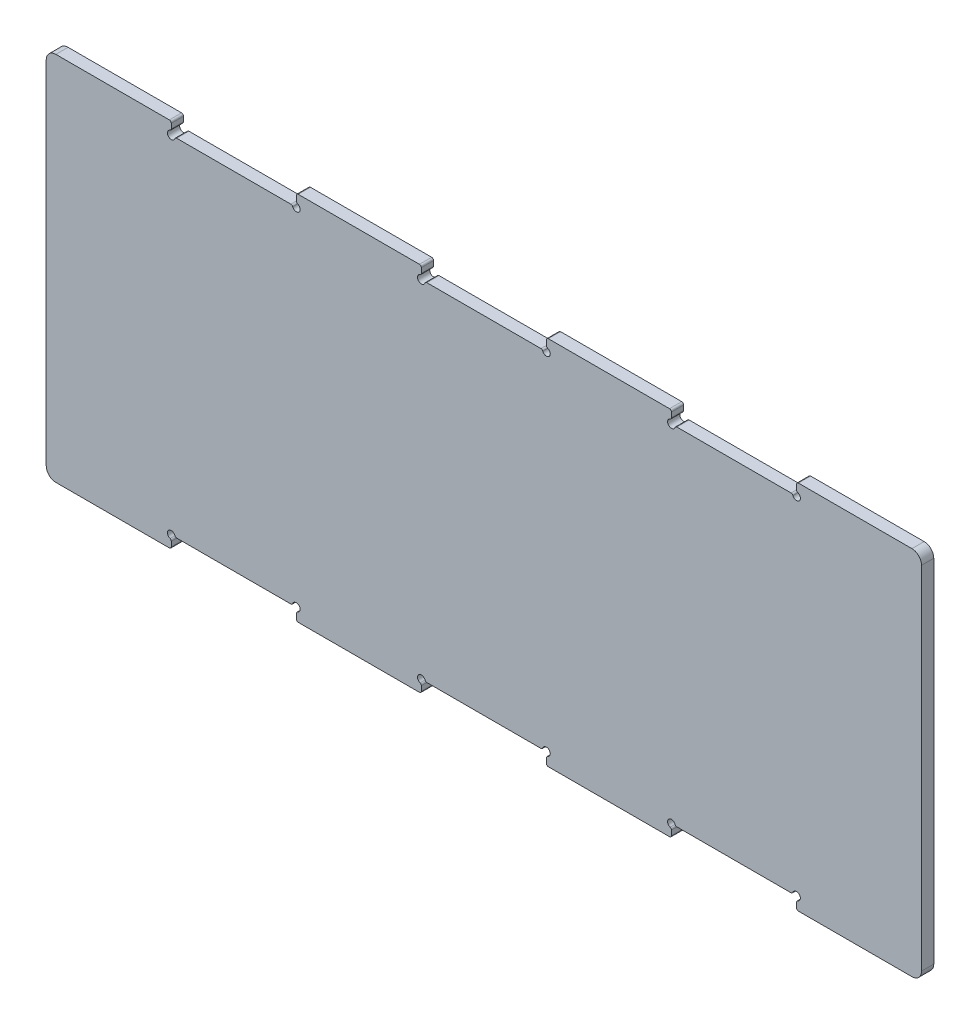
SolidWorks part; units mm, degrees
material "Pine"
ref_plane "Front Plane" through (0, 0, 0) normal (0, 0, 1) x (1, 0, 0)
ref_plane "Top Plane" through (0, 0, 0) normal (0, 1, 0) x (1, 0, 0)
ref_plane "Right Plane" through (0, 0, 0) normal (1, 0, 0) x (0, 0, -1)
sketch "Sketch1" plane through (0, 0, 0) normal (0, 0, 1) x (1, 0, 0)
  line L0 (0, 0) -> (455, 0)
  line L1 (0, 0) -> (0, 180)
  line L2 (455, 0) -> (455, 180)
  line L3 (0, 180) -> (455, 180)
  dimension "D1" = 455
  dimension "D2" = 180
extrude "Boss-Extrude1" add sketch "Sketch1" along normal mid plane 6.35
ref_plane "Plane1" through (0, 90, 0) normal (0, -1, 0) x (-1, 0, 0)
sketch "Sketch2" plane through (0, 0, 3.175) normal (0, 0, 1) x (1, 0, 0)
  line L0 (455, 0) -> (455, -6.35)
  line L1 (455, 0) -> (390, 0)
  line L2 (455, -6.35) -> (390, -6.35)
  line L3 (390, 0) -> (390, -6.35)
  dimension "D1" = 6.35
  dimension "D2" = 65
extrude "Boss-Extrude2" add sketch "Sketch2" against normal up to surface (6.35 mm away) up to face at (227.5, 90, -3.175)
pattern_linear "LPattern1" count 4 spacing 130 along (-1, 0, 0) of "Boss-Extrude2"
mirror "Mirror1" about plane through (0, 90, 0) normal (0, -1, 0) of "LPattern1", "Boss-Extrude2"
sketch "Sketch3" plane through (0, 0, 3.175) normal (0, 0, 1) x (1, 0, 0)
  circle A0 centre (325, 0) radius 2
  circle A1 centre (390, 0) radius 2
  dimension "D2" = 4
extrude "Cut-Extrude1" cut sketch "Sketch3" against normal through all
fillet "Fillet2" radius 1 2 edges at (390, -6.35, 0) (325, -6.35, 0)
sketch "Sketch4" plane through (0, 0, 3.175) normal (0, 0, 1) x (1, 0, 0)
  line L0 (390, -2) -> (390, -5.35) construction
  line L1 (327, 0) -> (388, 0) construction
  line L2 (325, -5.35) -> (325, -2) construction
  line L3 (390, -2.8284) -> (390, -5.35)
  line L4 (327.8284, 0) -> (387.1716, 0)
  line L5 (325, -5.35) -> (325, -2.8284)
  line L7 (391, -6.35) -> (324, -6.35)
  arc A0 (390, -2) -> (388, 0) centre (390, 0) ccw construction
  arc A1 (327, 0) -> (325, -2) centre (325, 0) ccw construction
  arc A2 (390.6667, -1.8856) -> (388.1144, 0.6667) centre (390, 0) ccw
  arc A3 (326.8856, 0.6667) -> (324.3333, -1.8856) centre (325, 0) ccw
  arc A4 (390, -5.35) -> (391, -6.35) centre (391, -5.35) ccw construction
  arc A5 (324, -6.35) -> (325, -5.35) centre (324, -5.35) ccw construction
  arc A6 (390, -5.35) -> (391, -6.35) centre (391, -5.35) ccw
  arc A7 (324, -6.35) -> (325, -5.35) centre (324, -5.35) ccw
  arc A8 (390, -2.8284) -> (390.6667, -1.8856) centre (391, -2.8284) cw
  arc A9 (388.1144, 0.6667) -> (387.1716, 0) centre (387.1716, 1) cw
  arc A10 (327.8284, 0) -> (326.8856, 0.6667) centre (327.8284, 1) cw
  arc A11 (324.3333, -1.8856) -> (325, -2.8284) centre (324, -2.8284) cw
  dimension "D1" = 1
extrude "Cut-Extrude2" cut sketch "Sketch4" against normal through all
pattern_linear "LPattern2" count 3 spacing 130 along (-1, 0, 0) of "Cut-Extrude2"
mirror "Mirror2" about plane through (0, 90, 0) normal (0, -1, 0) of "LPattern2", "Cut-Extrude2"
fillet "Fillet4" radius 5 4 edges at (455, 186.35, 0) (455, -6.35, 0) (0, 186.35, 0) (0, -6.35, 0)
